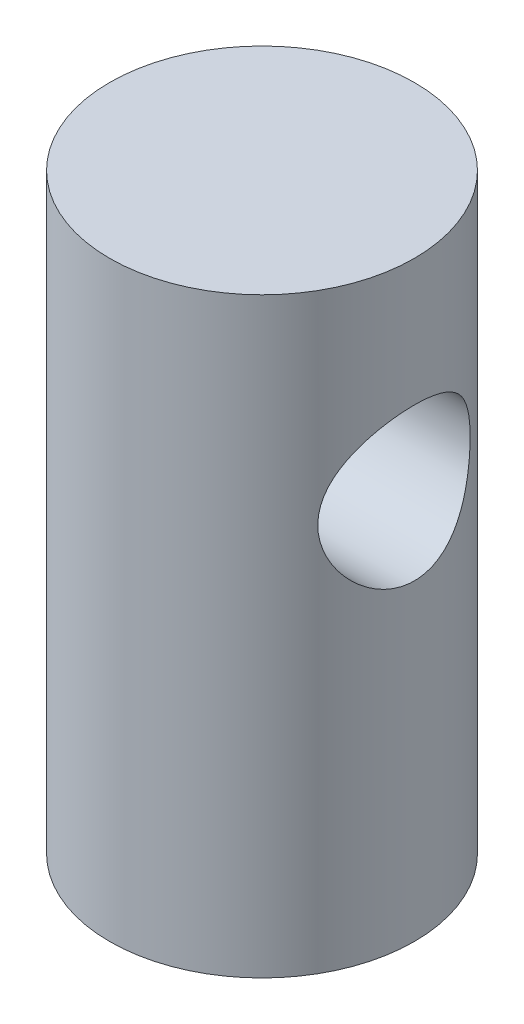
SolidWorks part; units mm, degrees
ref_plane "Front Plane" through (0, 0, 0) normal (0, 0, 1) x (1, 0, 0)
ref_plane "Top Plane" through (0, 0, 0) normal (0, 1, 0) x (1, 0, 0)
ref_plane "Right Plane" through (0, 0, 0) normal (1, 0, 0) x (0, 0, -1)
sketch "Sketch1" plane through (0, 0, 0) normal (0, 1, 0) x (1, 0, 0)
  circle A0 centre (0, 0) radius 3.81
  dimension "D1" = 7.62
extrude "Boss-Extrude1" add sketch "Sketch1" along normal blind 14.7955
ref_plane "Plane1" through (3.81, 0, 0) normal (1, 0, 0) x (0, 0, -1)
sketch "Sketch2" plane through (3.81, 0, 0) normal (1, 0, 0) x (0, 0, -1)
  line L0 (-3.81, 14.7955) -> (3.81, 14.7955) construction
  line L1 (0, 14.7955) -> (0, 0) construction
  line L2 (-3.81, 0) -> (3.81, 0) construction
  circle A0 centre (0, 9.7155) radius 1.905
  dimension "D1" = 3.81
  dimension "D2" = 5.08
extrude "Cut-Extrude1" cut sketch "Sketch2" against normal through all
